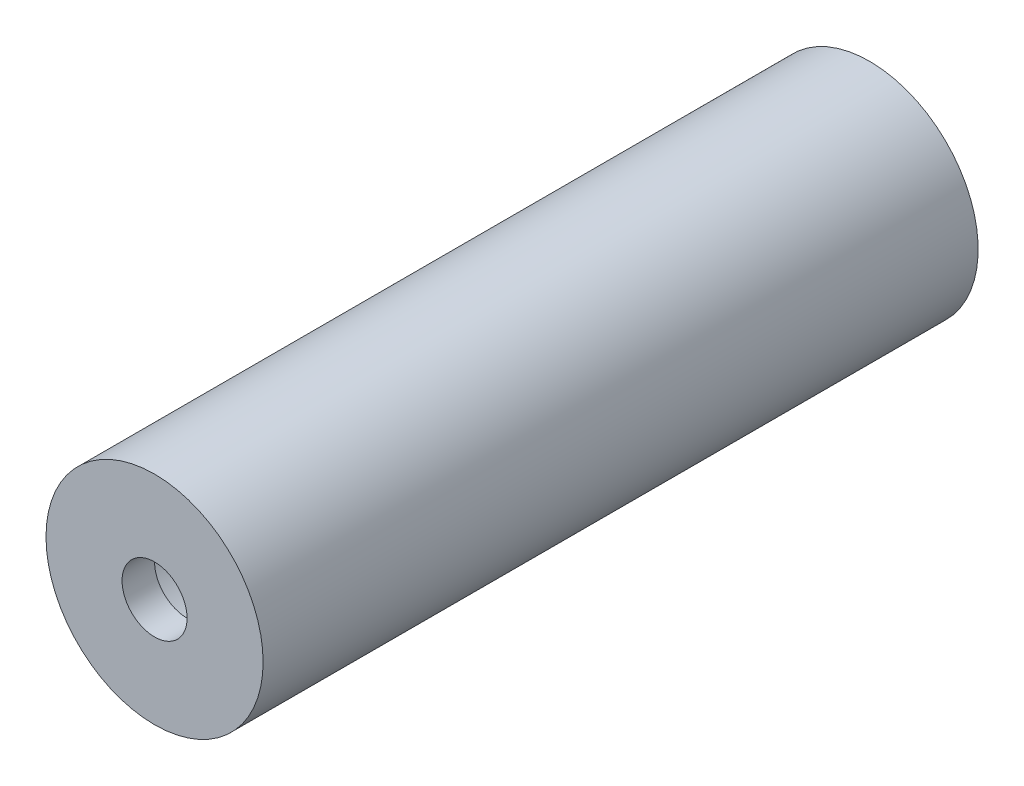
SolidWorks part; units mm, degrees
ref_plane "Front Plane" through (0, 0, 0) normal (0, 0, 1) x (1, 0, 0)
ref_plane "Top Plane" through (0, 0, 0) normal (0, 1, 0) x (1, 0, 0)
ref_plane "Right Plane" through (0, 0, 0) normal (1, 0, 0) x (0, 0, -1)
sketch "Sketch2" plane through (0, 0, 0) normal (0, 0, 1) x (1, 0, 0)
  circle A0 centre (0, 0) radius 12.85
  circle A1 centre (0, 0) radius 16.7
  dimension "D1" = 25.7
  dimension "D2" = 33.4
extrude "Boss-Extrude1" add sketch "Sketch2" along normal blind 100
sketch "Sketch3" plane through (0, 0, 0) normal (0, 0, -1) x (-1, 0, 0)
  circle A0 centre (0, 0) radius 16.7
extrude "Boss-Extrude2" add sketch "Sketch3" along normal blind 5
sketch "Sketch4" plane through (0, 0, 100) normal (0, 0, 1) x (1, 0, 0)
  circle A0 centre (0, 0) radius 16.7
  circle A1 centre (0, 0) radius 5
  dimension "D1" = 10
extrude "Boss-Extrude3" add sketch "Sketch4" along normal blind 5
